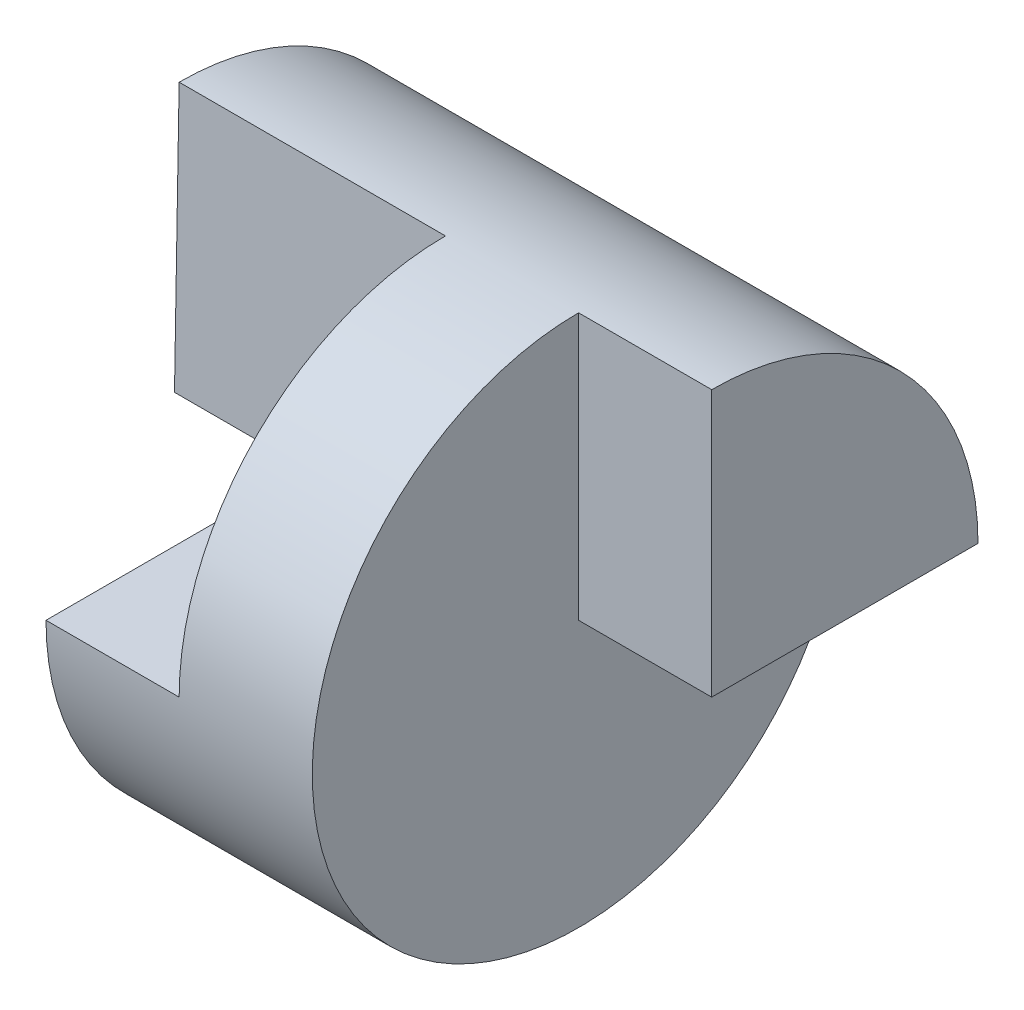
SolidWorks part; units mm, degrees
ref_plane "Front Plane" through (0, 0, 0) normal (0, 0, 1) x (1, 0, 0)
ref_plane "Top Plane" through (0, 0, 0) normal (0, 1, 0) x (1, 0, 0)
ref_plane "Right Plane" through (0, 0, 0) normal (1, 0, 0) x (0, 0, -1)
sketch "Sketch5" plane through (0, 0, 0) normal (0, 0, 1) x (1, 0, 0)
  line L0 (0, 0) -> (4, 0)
  dimension "D1" = 4
revolve "Revolve-Thin2" add sketch "Sketch5" angle 360 about L0 wall 2
sketch "Sketch6" plane through (0, 0, 0) normal (0, 0, 1) x (1, 0, 0)
  line L1 (0, 2) -> (1, 2)
  line L2 (0, 2) -> (0, 0)
  line L3 (0, 0) -> (1, 0)
  line L4 (1, 2) -> (1, 0)
  line L5 (4, 2) -> (3, 2)
  line L6 (4, 2) -> (4, 0)
  line L7 (4, 0) -> (3, 0)
  line L8 (3, 2) -> (3, 0)
  dimension "D1" = 1
  dimension "D2" = 1
  dimension "D3" = 2
  dimension "D4" = 2
extrude "Cut-Extrude5" cut sketch "Sketch6" against normal blind 11 contours L5 L8 L7 L6 | L4 L1 L2 L3
sketch "Sketch8" plane through (0, 0, 0) normal (0, 0, -1) x (-1, 0, 0)
  line L0 (0, 0) -> (-1, 0) construction
  line L1 (0, 2) -> (-0.5, 2)
  line L2 (0, 2) -> (0, 0)
  line L3 (0, 0) -> (-0.5, 0)
  line L4 (-0.5, 2) -> (-0.5, 0)
extrude "Cut-Extrude7" cut sketch "Sketch8" against normal blind 10
sketch "Sketch9" plane through (0, 0, 0) normal (0, 0, -1) x (-1, 0, 0)
  line L0 (-1, 2) -> (-3, 2) construction
  line L5 (-0.5, 0) -> (-2, 0)
  line L6 (-0.5, 0) -> (-0.5, 2)
  line L7 (-0.5, 2) -> (-2, 2)
  line L8 (-2, 0) -> (-2, 2)
  line L9 (-4, 2) -> (-4, 0) construction
  dimension "D1" = 2
extrude "Cut-Extrude8" cut sketch "Sketch9" against normal blind 10
sketch "Sketch10" plane through (4, 0, 0) normal (1, 0, 0) x (0, 0, -1)
  line L0 (2, 0) -> (-0.035, 0)
  line L1 (-0.035, 0) -> (0, 2)
  arc A0 (0, 2) -> (2, 0) centre (0, 0) cw
extrude "Boss-Extrude1" add sketch "Sketch10" against normal blind 4
sketch "Sketch13" plane through (0, 0, 0) normal (-1, 0, 0) x (0, 0, 1)
  line L1 (2, 0) -> (-2.4499, 0)
  line L2 (2, 0) -> (2, -3.1982)
  line L3 (2, -3.1982) -> (-2.4499, -3.1982)
  line L4 (-2.4499, 0) -> (-2.4499, -3.1982)
extrude "Cut-Extrude10" cut sketch "Sketch13" against normal blind 1
sketch "Sketch14" plane through (0, 0, 0) normal (0, 0, 1) x (1, 0, 0)
  line L1 (4, 2) -> (3, 2)
  line L2 (4, 2) -> (4, 0)
  line L3 (4, 0) -> (3, 0)
  line L4 (3, 2) -> (3, 0)
  dimension "D1" = 1
  dimension "D2" = 2
extrude "Cut-Extrude11" cut sketch "Sketch14" along normal blind 10
sketch "Sketch15" plane through (0, 0, 0) normal (0, 0, 1) x (1, 0, 0)
  line L1 (3, 0) -> (4, 0)
  line L2 (3, 0) -> (3, -2)
  line L3 (3, -2) -> (4, -2)
  line L4 (4, 0) -> (4, -2)
extrude "Cut-Extrude12" cut sketch "Sketch15" against normal mid plane 10
